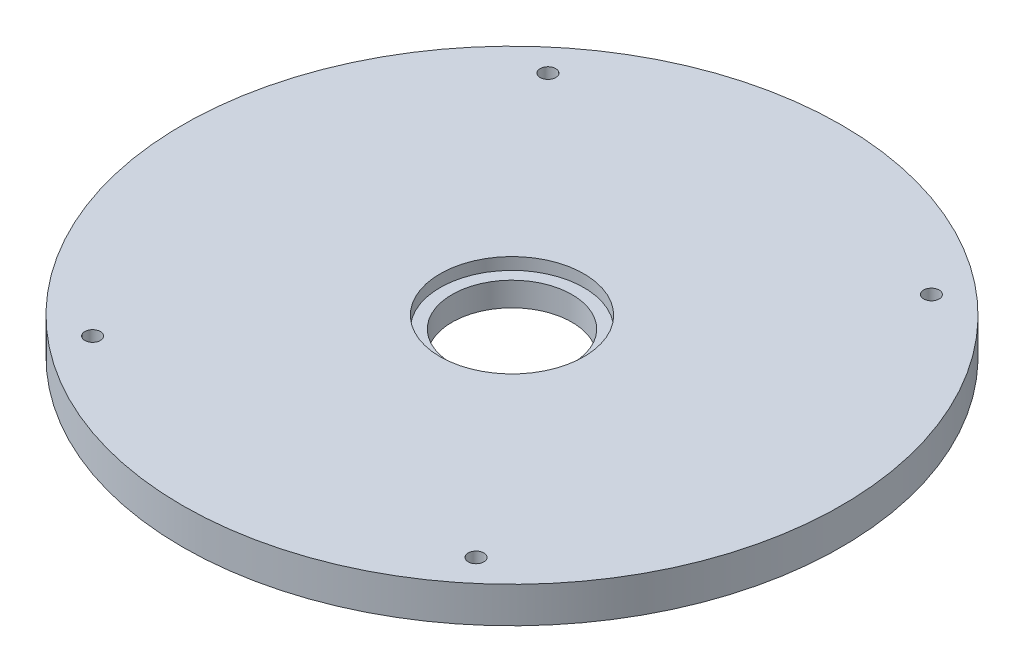
SolidWorks part; units mm, degrees
ref_plane "Front Plane" through (0, 0, 0) normal (0, 0, 1) x (1, 0, 0)
ref_plane "Top Plane" through (0, 0, 0) normal (0, 1, 0) x (1, 0, 0)
ref_plane "Right Plane" through (0, 0, 0) normal (1, 0, 0) x (0, 0, -1)
sketch "MountingHoles" plane through (0, 0, 0) normal (0, 1, 0) x (1, 0, 0)
  circle A0 centre (-80, 95) radius 3.25
  circle A1 centre (-80, -95) radius 3.25
  circle A2 centre (80, -95) radius 3.25
  circle A3 centre (80, 95) radius 3.25
  dimension "D1" = 6.5
  dimension "D2" = 190
  dimension "D3" = 160
  dimension "D4" = 80
  dimension "D5" = 95
sketch "BaseSketch" plane through (0, 0, 0) normal (0, 1, 0) x (1, 0, 0)
  circle A0 centre (0, 0) radius 137.5
  dimension "D1" = 275
extrude "Base" add sketch "BaseSketch" along normal blind 15
extrude "Cut-Extrude1" cut sketch "MountingHoles" along normal up to surface (15 mm away) up to face at (0, 15, 137.5)
sketch "BearingJ1" plane through (0, 0, 0) normal (0, 1, 0) x (1, 0, 0)
  circle A0 centre (0, 0) radius 25
  dimension "D1" = 50
extrude "Cut-Extrude3" cut sketch "BearingJ1" along direction (0, 1, 0) on the side of the normal up to next (15 mm away) contours A0
sketch "Sketch4" plane through (0, 15, 0) normal (0, 1, 0) x (1, 0, 0)
  line L1 (-62.5, -100) -> (62.5, -100) construction
  line L2 (-62.5, -100) -> (-62.5, 100) construction
  line L3 (-62.5, 100) -> (62.5, 100) construction
  line L4 (62.5, -100) -> (62.5, 100) construction
  line L5 (-62.5, -100) -> (62.5, 100) construction
  line L6 (-62.5, 100) -> (62.5, -100) construction
  circle A0 centre (0, 0) radius 75 construction
  dimension "D1" = 150
  dimension "D2" = 125
  dimension "D3" = 200
sketch "Sketch7" plane through (0, 15, 0) normal (0, 1, 0) x (1, 0, 0)
  line L0 (-62.5, -100) -> (-62.5, 100) construction
  line L1 (-62.5, 100) -> (62.5, 100) construction
  line L2 (-62.5, 80) -> (-62.5, 5) construction
  line L3 (0, 138.2666) -> (0, -138.2666) construction
  circle A0 centre (-62.5, 80) radius 3.5
  circle A1 centre (-62.5, 5) radius 3.5
  circle A2 centre (-62.5, -70) radius 3.5
  circle A3 centre (62.5, -70) radius 3.5
  circle A4 centre (62.5, 5) radius 3.5
  circle A5 centre (62.5, 80) radius 3.5
  point P14 (0, 0)
  dimension "D1" = 7
  dimension "D2" = 20
  dimension "D4" = 75
  dimension "D3" = 3
sketch "BearingRadialConstraint" plane through (0, 0, 0) normal (0, 1, 0) x (1, 0, 0)
  circle A0 centre (0, 0) radius 30
  dimension "D1" = 60
extrude "Cut-Extrude4" cut sketch "BearingRadialConstraint" against normal blind 5 from surface at 15 starting at face at (0, 15, 25)
